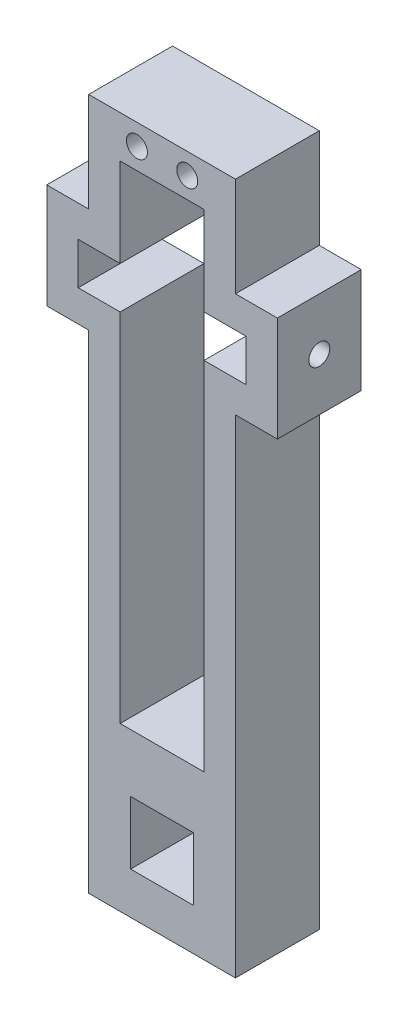
SolidWorks part; units mm, degrees
ref_plane "Front Plane" through (0, 0, 0) normal (0, 0, 1) x (1, 0, 0)
ref_plane "Top Plane" through (0, 0, 0) normal (0, 1, 0) x (1, 0, 0)
ref_plane "Right Plane" through (0, 0, 0) normal (1, 0, 0) x (0, 0, -1)
sketch "Sketch1" plane through (0, 0, 0) normal (0, 0, 1) x (1, 0, 0)
  line L0 (0, 27.5) -> (0, -9.1778) construction
  line L1 (3.5, -3.5) -> (-3.5, -3.5)
  line L2 (3.5, -3.5) -> (3.5, 3.5)
  line L3 (2, 4.2632) -> (-2, 4.2632)
  line L4 (-3.5, -3.5) -> (-3.5, 3.5)
  line L5 (3.5, -3.5) -> (-3.5, 3.5) construction
  line L6 (3.5, 3.5) -> (-3.5, -3.5) construction
  line L8 (-3.5, 3.5) -> (-3.5, 19.7632)
  line L9 (-2, 27.5) -> (2, 27.5)
  line L10 (3.5, 3.5) -> (3.5, 19.7632)
  line L11 (-2, 27.5) -> (-2, 23.2632)
  line L12 (2, 27.5) -> (2, 23.2632)
  line L13 (-3.5, 28.5) -> (3.5, 28.5) construction
  line L15 (-3.5, 27.5) -> (-3.5, 29.5)
  line L16 (-3.5, 29.5) -> (3.5, 29.5)
  line L17 (3.5, 27.5) -> (3.5, 29.5)
  line L18 (-8.0375, 22.2632) -> (10.367, 22.2632) construction
  line L19 (-1.5, -1.5) -> (1.5, -1.5)
  line L20 (-1.5, -1.5) -> (-1.5, 1.5)
  line L21 (-1.5, 1.5) -> (1.5, 1.5)
  line L22 (1.5, -1.5) -> (1.5, 1.5)
  line L23 (-1.5, -1.5) -> (1.5, 1.5) construction
  line L24 (-1.5, 1.5) -> (1.5, -1.5) construction
  line L25 (-2, 27.5) -> (-2, 17.7391) construction
  line L32 (-4, 26.4339) -> (-4, 19.7911) construction
  line L33 (-3.5, 24.7632) -> (-3.5, 27.5)
  line L34 (-3.5, 19.7632) -> (-5.5, 19.7632)
  line L36 (-3.5, 24.7632) -> (-5.5, 24.7632)
  line L37 (-5.5, 19.7632) -> (-5.5, 24.7632)
  line L42 (-4, 23.2632) -> (-2, 23.2632)
  line L44 (-4, 21.2632) -> (-4, 23.2632)
  line L47 (-4, 21.2632) -> (-2, 21.2632)
  line L48 (4, 21.2632) -> (4, 23.2632)
  line L49 (3.5, 24.7632) -> (5.5, 24.7632)
  line L50 (3.5, 19.7632) -> (5.5, 19.7632)
  line L51 (5.5, 19.7632) -> (5.5, 24.7632)
  line L52 (4, 21.2632) -> (2, 21.2632)
  line L53 (4, 23.2632) -> (2, 23.2632)
  line L54 (-2, 21.2632) -> (-2, 4.2632)
  line L55 (2, 21.2632) -> (2, 4.2632)
  line L56 (3.5, 24.7632) -> (3.5, 27.5)
  circle A0 centre (-1.2, 28.5) radius 0.5
  circle A1 centre (1.2, 28.5) radius 0.5
  point P0 (0, 0)
  point P22 (0, 0)
  point P29 (0, 22.2632)
  point P47 (-4, 22.2632)
  point P48 (-5.5, 22.2632)
  dimension "D6" = 1
  dimension "D2" = 1.5
  dimension "D3" = 24
  dimension "D4" = 2
  dimension "D5" = 2
  dimension "D7" = 1.2
  dimension "D8" = 3
  dimension "D9" = 18
  dimension "D10" = 1.5
  dimension "D11" = 1.5
  dimension "D15" = 5
extrude "Boss-Extrude1" add sketch "Sketch1" along normal blind 4
sketch "草图1" plane through (-5.5, 0, 0) normal (-1, 0, 0) x (0, 0, 1)
  line L0 (0, 22.2632) -> (4, 22.2632) construction
  line L1 (0, 24.7632) -> (0, 19.7632) construction
  line L2 (4, 24.7632) -> (4, 19.7632) construction
  circle A0 centre (2, 22.2632) radius 0.5
  dimension "D1" = 1
extrude "切除-拉伸1" cut sketch "草图1" against normal through all
